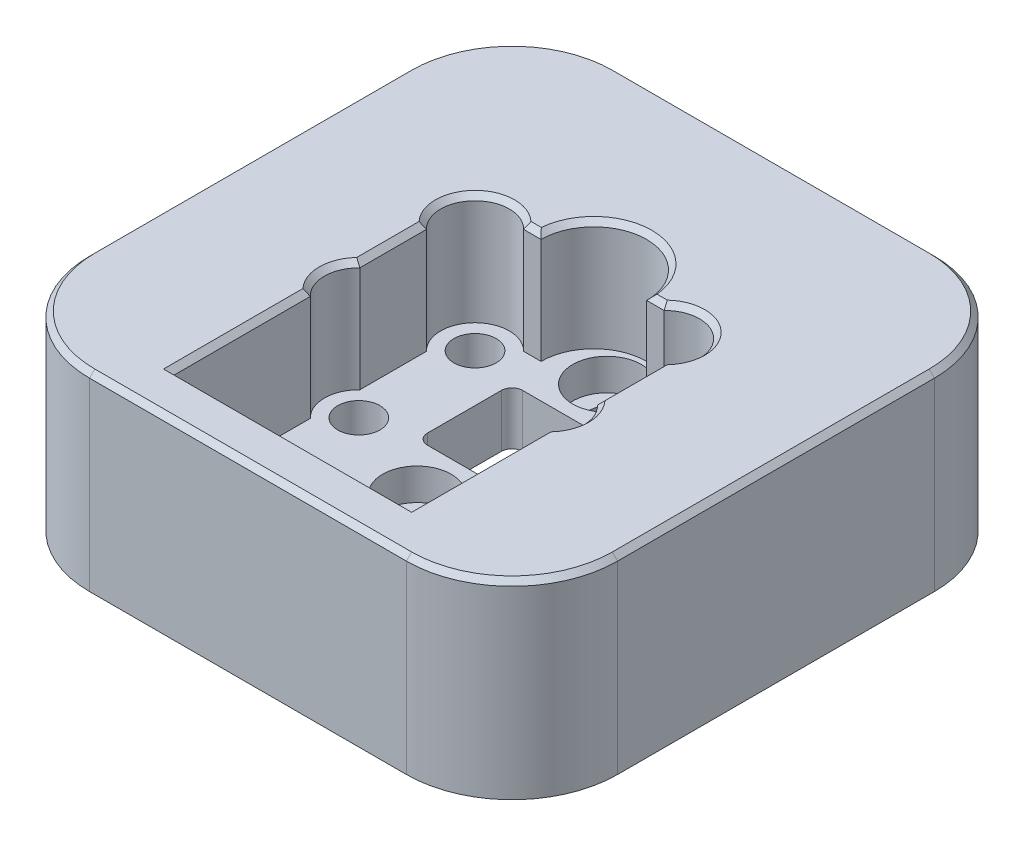
SolidWorks part; units mm, degrees
ref_plane "Front Plane" through (0, 0, 0) normal (0, 0, 1) x (1, 0, 0)
ref_plane "Top Plane" through (0, 0, 0) normal (0, 1, 0) x (1, 0, 0)
ref_plane "Right Plane" through (0, 0, 0) normal (1, 0, 0) x (0, 0, -1)
sketch "Sketch2" plane through (0, 0, 0) normal (0, 1, 0) x (1, 0, 0)
  line L1 (25, -25) -> (-25, -25)
  line L2 (25, -25) -> (25, 25)
  line L3 (25, 25) -> (-25, 25)
  line L4 (-25, -25) -> (-25, 25)
  line L5 (25, -25) -> (-25, 25) construction
  line L6 (25, 25) -> (-25, -25) construction
  point P0 (0, 0)
  dimension "D1" = 50
  dimension "D2" = 50
extrude "Boss-Extrude1" add sketch "Sketch2" along normal blind 10
sketch "Sketch3" plane through (0, 10, 0) normal (0, 1, 0) x (1, 0, 0)
  line L1 (-4.5, -4.5) -> (4.5, -4.5)
  line L2 (-4.5, -4.5) -> (-4.5, 4.5)
  line L3 (-4.5, 4.5) -> (4.5, 4.5)
  line L4 (4.5, -4.5) -> (4.5, 4.5)
  line L5 (-4.5, -4.5) -> (4.5, 4.5) construction
  line L6 (-4.5, 4.5) -> (4.5, -4.5) construction
  point P0 (0, 0)
  dimension "D1" = 9
  dimension "D2" = 9
extrude "Cut-Extrude1" cut sketch "Sketch3" against normal up to surface (10 mm away) up to face at (0, 0, 0)
sketch "Sketch4" plane through (0, 0, 0) normal (0, -1, 0) x (1, 0, 0)
  circle A0 centre (0, 0) radius 23.125
  dimension "D1" = 46.25
extrude "Cut-Extrude2" cut sketch "Sketch4" against normal blind 2.5
hole_wizard "Ø4.0mm Dowel Hole1" positions "Sketch8" profile "Sketch9" hole size "Ø4.0" standard "ANSI Metric" end condition through all
sketch "Sketch8" plane through (0, 10, 0) normal (0, 1, 0) x (1, 0, 0)
  line L0 (-9, 5.5) -> (9, 5.5) construction
  line L1 (9, 5.5) -> (9, -5.5) construction
  line L2 (9, -5.5) -> (-9, -5.5) construction
  line L3 (-9, -5.5) -> (-9, 5.5) construction
  point P0 (-9, 5.5)
  point P2 (9, 5.5)
  point P4 (9, -5.5)
  point P6 (-9, -5.5)
  point P18 (0, 5.5)
  point P20 (-9, 0)
  dimension "D1" = 18
  dimension "D2" = 11
sketch "Sketch9" plane through (-9, 10, -5.5) normal (1, 0, 0) x (0, 0, 1)
  line L0 (0, 0) -> (0, 10)
  line L1 (0, 10) -> (2, 10)
  line L2 (2, 10) -> (2, 0)
  line L5 (2, 0) -> (0, 0)
  line L11 (0, -6.35) -> (0, 107.95) construction
  dimension "Thru Hole Dia." = 4
  dimension "Thru Hole Depth" = 10
hole_wizard "CBORE for M3 SHCS1" [suppressed] positions "Sketch15" profile "Sketch16" counterbore size "M3" standard "ANSI Metric"
sketch "Sketch15" plane through (0, 10, 0) normal (0, 1, 0) x (1, 0, 0)
  line L0 (0, 9) -> (0, -9) construction
  point P0 (0, 9)
  point P2 (0, -9)
  point P9 (0, 0)
  dimension "D1" = 18
sketch "Sketch16" plane through (0, 10, -9) normal (1, 0, 0) x (0, 0, 1)
  line L0 (0, 0) -> (0, 8.5215)
  line L1 (0, 8.5215) -> (1.7, 7.5)
  line L2 (1.7, 7.5) -> (1.7, 3)
  line L3 (1.7, 3) -> (3.25, 3)
  line L4 (3.25, 3) -> (3.25, 0)
  line L5 (3.25, 0) -> (0, 0)
  line L10 (0, 8.5215) -> (-1.7, 7.5) construction
  line L11 (0, -6.35) -> (0, 107.95) construction
  dimension "Hole Dia." = 3.4
  dimension "Hole Depth" = 7.5
  dimension "C'Bore Dia." = 6.5
  dimension "C'Bore Depth" = 3
  dimension "Drill Angle" = 118
fillet "Fillet1" radius 1 4 edges at (4.5, 6.25, 4.5) (-4.5, 6.25, 4.5) (-4.5, 6.25, -4.5) (4.5, 6.25, -4.5)
fillet "Fillet2" radius 10 4 edges at (25, 5, 25) (25, 5, -25) (-25, 5, 25) (-25, 5, -25)
sketch "Sketch17" plane through (0, 10, 0) normal (0, 1, 0) x (1, 0, 0)
  line L0 (5, 7.75) -> (11.25, 7.75)
  line L1 (-11.25, 7.75) -> (-5, 7.75)
  line L2 (-11.25, 7.75) -> (-11.25, -20.75)
  line L3 (-11.25, -20.75) -> (11.25, -20.75)
  line L4 (11.25, 7.75) -> (11.25, -20.75)
  arc A2 (5, 7.75) -> (-5, 7.75) centre (0, 7.75) ccw
  dimension "D3" = 7.75
  dimension "D4" = 5
  dimension "D1" = 22.5
  dimension "D2" = 28.5
  dimension "D5" = 6.25
extrude "Cut-Extrude3" cut sketch "Sketch17" against normal blind 2.5
hole_wizard "CBORE for M3 SHCS2" positions "Sketch18" profile "Sketch19" counterbore size "M3" standard "ANSI Metric" end condition through all
sketch "Sketch18" plane through (0, 7.5, 0) normal (0, 1, 0) x (1, 0, 0)
  line L0 (0, -9) -> (0, 9) construction
  point P0 (0, -9)
  point P2 (0, 9)
  point P9 (0, 0)
  dimension "D1" = 18
sketch "Sketch19" plane through (0, 7.5, 9) normal (1, 0, 0) x (0, 0, 1)
  line L0 (0, 0) -> (0, 7.5)
  line L1 (0, 7.5) -> (1.7, 7.5)
  line L3 (1.7, 7.5) -> (1.7, 3)
  line L4 (1.7, 3) -> (3.25, 3)
  line L5 (3.25, 3) -> (3.25, 0)
  line L7 (3.25, 0) -> (0, 0)
  line L11 (0, -6.35) -> (0, 107.95) construction
  dimension "Thru Hole Dia." = 3.4
  dimension "Thru Hole Depth" = 7.5
  dimension "C'Bore Dia." = 6.5
  dimension "C'Bore Depth" = 3
sketch "Sketch20" plane through (0, 10, 0) normal (0, 1, 0) x (1, 0, 0)
  circle A0 centre (0, 9) radius 3.25 construction
  circle A1 centre (0, 9) radius 3.25
extrude "Cut-Extrude4" [suppressed] cut sketch "Sketch20" against normal up to surface (2.5 mm away)
sketch "Sketch21" plane through (0, 10, 0) normal (0, 1, 0) x (1, 0, 0)
  circle A0 centre (-9, 5.5) radius 3.25
  circle A1 centre (9, 5.5) radius 3.25
  circle A2 centre (9, -5.5) radius 3.25
  circle A3 centre (-9, -5.5) radius 3.25
  dimension "D1" = 6.5
  dimension "D2" = 6.5
  dimension "D3" = 6.5
  dimension "D4" = 6.5
extrude "Cut-Extrude5" cut sketch "Sketch21" against normal up to surface (2.5 mm away) up to face at (0, 7.5, 12.25)
sketch "Sketch22" plane through (0, 10, 0) normal (0, 1, 0) x (1, 0, 0)
  line L0 (-11.25, 3.1548) -> (-11.25, -3.1548) construction
  line L1 (-11.25, -7.8452) -> (-11.25, -20.75) construction
  line L2 (-11.25, -20.75) -> (11.25, -20.75) construction
  line L3 (11.25, -20.75) -> (11.25, -7.8452) construction
  line L4 (-15, -25) -> (15, -25)
  line L5 (25, -15) -> (25, 15)
  line L6 (15, 25) -> (-15, 25)
  line L7 (-25, 15) -> (-25, -15)
  line L8 (-15, -25) -> (15, -25)
  line L9 (25, -15) -> (25, 15)
  line L10 (15, 25) -> (-15, 25)
  line L11 (-25, 15) -> (-25, -15)
  line L12 (11.25, -3.1548) -> (11.25, 3.1548) construction
  line L19 (-11.25, 3.1548) -> (-11.25, -3.1548)
  line L20 (-11.25, -7.8452) -> (-11.25, -20.75)
  line L21 (-11.25, -20.75) -> (11.25, -20.75)
  line L22 (11.25, -20.75) -> (11.25, -7.8452)
  line L23 (11.25, -3.1548) -> (11.25, 3.1548)
  line L32 (6.6548, 7.75) -> (5, 7.75) construction
  line L33 (-5, 7.75) -> (-6.6548, 7.75) construction
  line L36 (6.6548, 7.75) -> (5, 7.75)
  line L37 (-5, 7.75) -> (-6.6548, 7.75)
  arc A2 (-11.25, -3.1548) -> (-11.25, -7.8452) centre (-9, -5.5) ccw construction
  arc A3 (11.25, -7.8452) -> (11.25, -3.1548) centre (9, -5.5) ccw construction
  arc A4 (15, -25) -> (25, -15) centre (15, -15) ccw
  arc A5 (25, 15) -> (15, 25) centre (15, 15) ccw
  arc A6 (-15, 25) -> (-25, 15) centre (-15, 15) ccw
  arc A7 (-25, -15) -> (-15, -25) centre (-15, -15) ccw
  arc A8 (15, -25) -> (25, -15) centre (15, -15) ccw
  arc A9 (25, 15) -> (15, 25) centre (15, 15) ccw
  arc A10 (-15, 25) -> (-25, 15) centre (-15, 15) ccw
  arc A11 (-25, -15) -> (-15, -25) centre (-15, -15) ccw
  arc A16 (-11.25, -3.1548) -> (-11.25, -7.8452) centre (-9, -5.5) ccw
  arc A17 (11.25, -7.8452) -> (11.25, -3.1548) centre (9, -5.5) ccw
  arc A23 (5, 7.75) -> (-5, 7.75) centre (0, 7.75) ccw construction
  arc A26 (5, 7.75) -> (-5, 7.75) centre (0, 7.75) ccw
  arc A28 (-6.6548, 7.75) -> (-11.25, 3.1548) centre (-9, 5.5) ccw construction
  arc A29 (11.25, 3.1548) -> (6.6548, 7.75) centre (9, 5.5) ccw construction
  arc A30 (-6.6548, 7.75) -> (-11.25, 3.1548) centre (-9, 5.5) ccw
  arc A31 (11.25, 3.1548) -> (6.6548, 7.75) centre (9, 5.5) ccw
  dimension "D1" = 0
extrude "Boss-Extrude2" add sketch "Sketch22" along normal blind 8
chamfer "Chamfer1" distance 0.5 angle 45 20 edges at (-12.25, 18, 5.5) (-11.25, 18, 14.2976) (0, 18, 20.75) (11.25, 18, 14.2976) (12.25, 18, 5.5) (11.25, 18, 0) (-11.25, 18, 0) (-5.8274, 18, -7.75) (5.8274, 18, -7.75) (-25, 18, 0) (-22.0711, 18, -22.0711) (0, 18, -25) (22.0711, 18, -22.0711) (25, 18, 0) (22.0711, 18, 22.0711) (0, 18, 25) (-22.0711, 18, 22.0711) (0, 18, -12.75) (11.2981, 18, -7.7981) (-11.2981, 18, -7.7981)
equation "\"D2@Sketch2\"=\"D1@Sketch2\""
equation "\"D2@Sketch3\"=\"D1@Sketch3\""
equation "\"D2@Sketch21\"=\"D1@Sketch21\""
equation "\"D3@Sketch21\"=\"D1@Sketch21\""
equation "\"D4@Sketch21\"=\"D1@Sketch21\""
